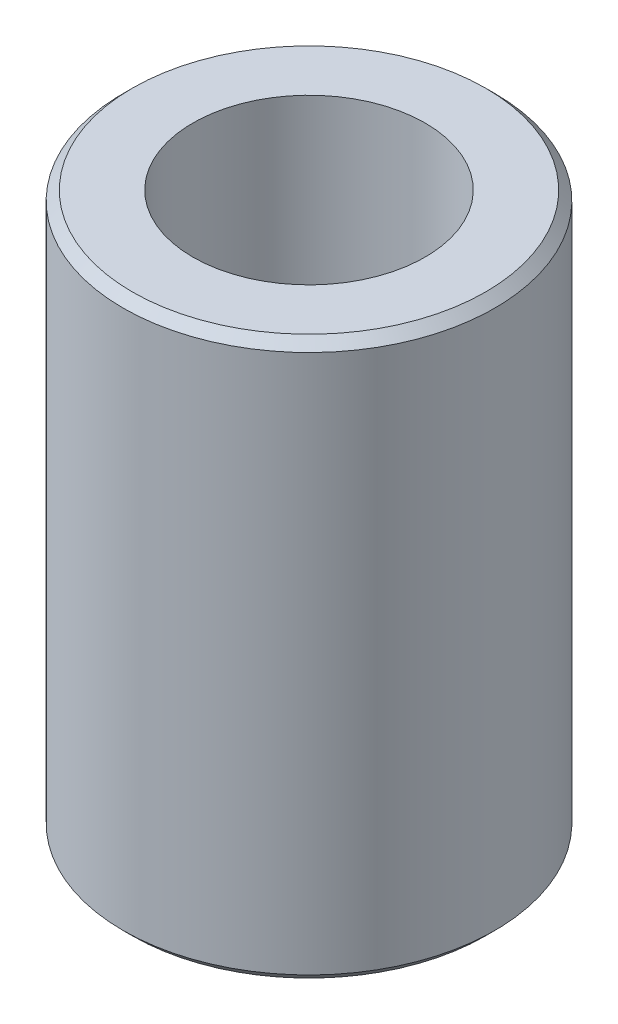
SolidWorks part; units mm, degrees
ref_plane "Front Plane" through (0, 0, 0) normal (0, 0, 1) x (1, 0, 0)
ref_plane "Top Plane" through (0, 0, 0) normal (0, 1, 0) x (1, 0, 0)
ref_plane "Right Plane" through (0, 0, 0) normal (1, 0, 0) x (0, 0, -1)
sketch "Sketch1" plane through (0, 0, 0) normal (0, 1, 0) x (1, 0, 0)
  circle A0 centre (0, 0) radius 20
  circle A1 centre (0, 0) radius 12.5
  dimension "D1" = 40
  dimension "D2" = 25
extrude "Boss-Extrude1" add sketch "Sketch1" along normal blind 60
chamfer "Chamfer1" distance 1 angle 45 2 edges at (0, 0, 20) (0, 60, 20)
